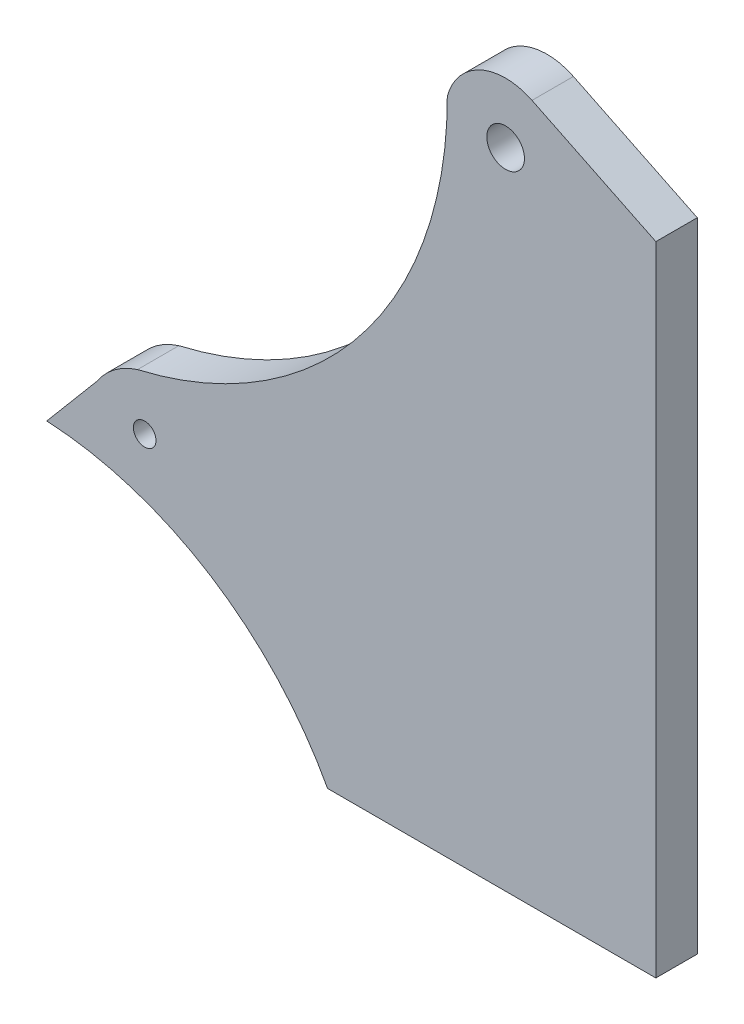
SolidWorks part; units mm, degrees
ref_plane "Front" through (0, 0, 0) normal (0, 0, 1) x (1, 0, 0)
ref_plane "Top" through (0, 0, 0) normal (0, 1, 0) x (1, 0, 0)
ref_plane "Right" through (0, 0, 0) normal (1, 0, 0) x (0, 0, -1)
sketch "Sketch1" plane through (0, 0, 0) normal (0, 0, 1) x (1, 0, 0)
  line L0 (0, 0) -> (436, 0)
  line L1 (436, 0) -> (436, 847)
  line L2 (436, 847) -> (271.5207, 927.2219)
  line L5 (-306.7686, 314.7247) -> (-372.9877, 236.2151)
  arc A0 (271.5207, 927.2219) -> (159.0098, 875.3897) centre (236.451, 855.3184) ccw
  arc A1 (159.0098, 875.3897) -> (-252.4563, 355.5904) centre (-372.9877, 873.7566) cw
  arc A2 (-252.4563, 355.5904) -> (-306.7686, 314.7247) centre (-223.0672, 260.0065) ccw
  arc A3 (-372.9877, 236.2151) -> (0, 0) centre (-396.3004, -213.1807) cw
  circle A4 centre (236.451, 855.3184) radius 25
  circle A5 centre (-242.8948, 286.2151) radius 15
  dimension "D5" = 80
  dimension "D6" = 532
  dimension "D7" = 100
  dimension "D8" = 450
  dimension "D16" = 50
  dimension "D17" = 30
  dimension "D1" = 436
  dimension "D2" = 847
  dimension "D3" = 183
  dimension "D4" = 116
  dimension "D9" = 102.707
  dimension "D10" = 20.0714
  dimension "D11" = 355.5904
  dimension "D12" = 314.7247
  dimension "D13" = 236.2151
  dimension "D14" = 252.4563
  dimension "D15" = 306.7686
  dimension "D18" = 130.0929
  dimension "D19" = 50
extrude "Boss-Extrude1" add sketch "Sketch1" along normal blind 55
